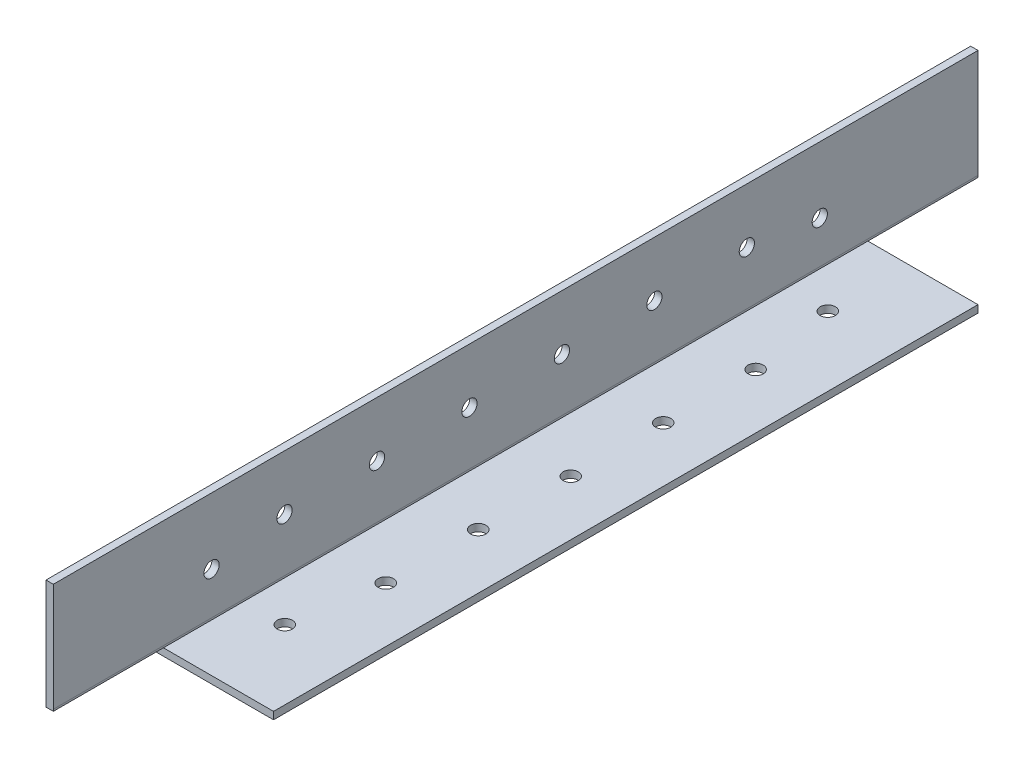
SolidWorks part; units mm, degrees
material "6061 Alloy"
ref_plane "Front Plane" through (0, 0, 0) normal (0, 0, 1) x (1, 0, 0)
ref_plane "Top Plane" through (0, 0, 0) normal (0, 1, 0) x (1, 0, 0)
ref_plane "Right Plane" through (0, 0, 0) normal (1, 0, 0) x (0, 0, -1)
sketch "Sketch1" plane through (0, 0, 0) normal (0, 0, 1) x (1, 0, 0)
  line L0 (0, 25.4) -> (0, 0) construction
  line L1 (0, 0) -> (25.4, 0) construction
  line L2 (25.4, 0) -> (25.4, 1.5875) construction
  line L3 (25.4, 1.5875) -> (1.5875, 1.5875) construction
  line L4 (1.5875, 1.5875) -> (1.5875, 25.4) construction
  line L6 (1.5875, 25.4) -> (0, 25.4) construction
  arc A0 (1.5875, 1.8415) -> (1.8415, 1.5875) centre (1.8415, 1.8415) ccw construction
  point P4 (0, 0)
  dimension "Inside Corner Radius" = 0.254
  dimension "Outside Height" = 25.4
  dimension "Inside Height" = 23.8125
  dimension "Outside Width" = 25.4
  dimension "Inside Width" = 23.8125
  dimension "Wall Thickness" = 1.5875
  dimension "Shape" = 90
sketch "Sketch2" plane through (0, 0, 0) normal (1, 0, 0) x (0, 0, -1)
  line L0 (1219.2, 0) -> (-1219.2, 0) construction
  line L1 (-1219.2, 25.4) -> (-1219.2, 0) construction
  line L2 (1219.2, 25.4) -> (1219.2, 0) construction
  point P0 (-1189.99, 0)
  point P4 (0, 0)
  point P6 (1189.99, 0)
  dimension "D1" = 29.21
  dimension "D2" = 29.21
  dimension "D3" = 25.4
  dimension "Length" = 2438.4
sketch "Sketch3" plane through (0, 0, 0) normal (0, 0, 1) x (1, 0, 0)
  line L0 (1.5875, 25.4) -> (0, 25.4)
  line L1 (0, 25.4) -> (0, 0)
  line L2 (0, 0) -> (25.4, 0)
  line L3 (25.4, 0) -> (25.4, 1.5875)
  line L4 (25.4, 1.5875) -> (1.5875, 1.5875)
  line L5 (1.5875, 1.5875) -> (1.5875, 25.4)
extrude "Boss-Extrude1" add sketch "Sketch3" along normal mid plane 2438.4
fillet "Fillet1" radius 0.254 1 edges at (1.5875, 1.5875, 0)
sketch "Sketch4" plane through (0, 0, 0) normal (-1, 0, 0) x (0, 0, 1)
  line L0 (1219.2, 25.4) -> (1219.2, 0) construction
  line L1 (-1219.2, 0) -> (1019.2, 0)
  line L2 (-1219.2, 0) -> (-1219.2, 74.9453)
  line L3 (-1219.2, 74.9453) -> (1019.2, 74.9453)
  line L4 (1019.2, 0) -> (1019.2, 74.9453)
  dimension "D1" = 200
extrude "Cut-Extrude1" cut sketch "Sketch4" against normal blind 60
sketch "Sketch8" plane through (0, 1.5875, 0) normal (0, 1, 0) x (1, 0, 0)
  line L0 (25.4, -1119.2) -> (1.5875, -1119.2) construction
  line L1 (25.4, -1219.2) -> (1.587, -1219.2)
  line L2 (25.4, -1219.2) -> (25.4, -1195.387)
  line L3 (25.4, -1195.387) -> (1.587, -1195.387)
  line L4 (1.587, -1219.2) -> (1.587, -1195.387)
  line L5 (25.4, -1219.2) -> (25.4, -1019.2) construction
  line L6 (1.5875, -1219.2) -> (1.5875, -1019.2) construction
  line L7 (25.4, -1043.013) -> (1.587, -1043.013)
  line L8 (1.587, -1019.2) -> (1.587, -1043.013)
  line L9 (25.4, -1019.2) -> (1.587, -1019.2)
  line L10 (25.4, -1019.2) -> (25.4, -1043.013)
  dimension "D1" = 23.813
extrude "Cut-Extrude6" cut sketch "Sketch8" against normal blind 28.313
sketch "Sketch9" plane through (0, 0, 1019.2) normal (0, 0, -1) x (-1, 0, 0)
  line L0 (-1.8415, 1.5875) -> (-1.587, 1.5875)
  line L1 (-1.587, 1.5875) -> (-1.5875, 1.9903)
  line L2 (-1.5875, 1.8415) -> (-1.5875, 25.4) construction
  line L3 (-1.5875, 1.9903) -> (-1.8415, 1.9903)
  line L4 (-1.8415, 1.9903) -> (-1.8415, 1.5875)
extrude "Cut-Extrude7" cut sketch "Sketch9" against normal blind 228.313
sketch "Sketch10" plane through (0, 0, 0) normal (-1, 0, 0) x (0, 0, 1)
  line L0 (1119.2, 25.4) -> (1119.2, 0) construction
  line L1 (1219.2, 25.4) -> (1195.387, 25.4)
  line L2 (1219.2, 25.4) -> (1219.2, 1.587)
  line L3 (1219.2, 1.587) -> (1195.387, 1.587)
  line L4 (1195.387, 25.4) -> (1195.387, 1.587)
  line L5 (1195.387, 1.587) -> (1219.2, 1.587)
  line L6 (1195.387, 1.587) -> (1195.387, 0)
  line L7 (1195.387, 0) -> (1219.2, 0)
  line L8 (1219.2, 1.587) -> (1219.2, 0)
  line L9 (1219.2, 25.4) -> (1019.2, 25.4) construction
  line L10 (1219.2, 0) -> (1019.2, 0) construction
  line L11 (1043.013, 0) -> (1019.2, 0)
  line L12 (1019.2, 1.587) -> (1019.2, 0)
  line L13 (1043.013, 1.587) -> (1019.2, 1.587)
  line L14 (1043.013, 1.587) -> (1043.013, 0)
  line M11 (1019.2, 0) -> (1219.2, 0)
  line M12 (1219.2, 0) -> (1219.2, 25.4)
  dimension "D1" = 23.813
  dimension "D2" = 23.813
extrude "Cut-Extrude8" cut sketch "Sketch10" against normal blind 228.313 contours L3 L6 M11 M12 | L11 L12 L13 L14
sketch "Sketch14" plane through (0, 1.5875, 0) normal (0, 1, 0) x (1, 0, 0)
  line L0 (25.4, -1159.2003) -> (1.5875, -1159.2003) construction
  line L1 (25.4, -1195.387) -> (25.4, -1043.013) construction
  line L2 (1.5875, -1219.2) -> (1.5875, -1019.2) construction
  line L3 (10.3759, -1177.925) -> (10.3759, -1159.2003) construction
  line L4 (25.4, -1079.2003) -> (1.5875, -1079.2003) construction
  line L5 (10.3759, -1060.4755) -> (10.3759, -1079.2003) construction
  circle A0 centre (10.3759, -1177.925) radius 1.65
  circle A1 centre (10.3759, -1060.4755) radius 1.65
  circle A2 centre (13.4937, -1079.2003) radius 1.65
  circle A3 centre (13.4938, -1099.2003) radius 1.65
  circle A4 centre (13.4938, -1119.2003) radius 1.65
  circle A5 centre (13.4938, -1139.2003) radius 1.65
  circle A6 centre (13.4938, -1159.2003) radius 1.65
  dimension "D1" = 3.3
  dimension "D3" = 20
  dimension "D2" = 5
extrude "Cut-Extrude11" cut sketch "Sketch14" against normal blind 60
sketch "Sketch15" plane through (1.5875, 0, 0) normal (1, 0, 0) x (0, 0, -1)
  line L0 (-1069.2, 1.5875) -> (-1069.2, 25.4) construction
  line L1 (-1195.387, 1.5875) -> (-1043.013, 1.5875) construction
  line L2 (-1219.2, 25.4) -> (-1019.2, 25.4) construction
  line L3 (-1053.4212, 11.1125) -> (-1069.2, 11.1125) construction
  line L4 (-1184.9788, 11.1125) -> (-1184.9788, 25.4) construction
  line L5 (-1169.2, 13.4937) -> (-1184.9788, 13.4937) construction
  circle A0 centre (-1184.9788, 11.1125) radius 1.65
  circle A1 centre (-1053.4212, 11.1125) radius 1.65
  circle A2 centre (-1069.2, 13.4938) radius 1.65
  circle A3 centre (-1089.2, 13.4938) radius 1.65
  circle A4 centre (-1109.2, 13.4938) radius 1.65
  circle A5 centre (-1129.2, 13.4938) radius 1.65
  circle A6 centre (-1149.2, 13.4938) radius 1.65
  circle A7 centre (-1169.2, 13.4937) radius 1.65
  dimension "D1" = 3.3
  dimension "D3" = 20
  dimension "D2" = 6
extrude "Cut-Extrude12" cut sketch "Sketch15" against normal blind 60
equation "\"D1@Boss-Extrude1\"=\"Length@Sketch2\""
equation "\"D1@Sketch2\" = \"Outside Width@Sketch1\" * 1.15"
equation "\"D2@Sketch2\"=\"D1@Sketch2\""
equation "\"D1@Fillet1\"=\"Inside Corner Radius@Sketch1\""
equation "\"D3@Sketch2\"=\"Outside Height@Sketch1\""
